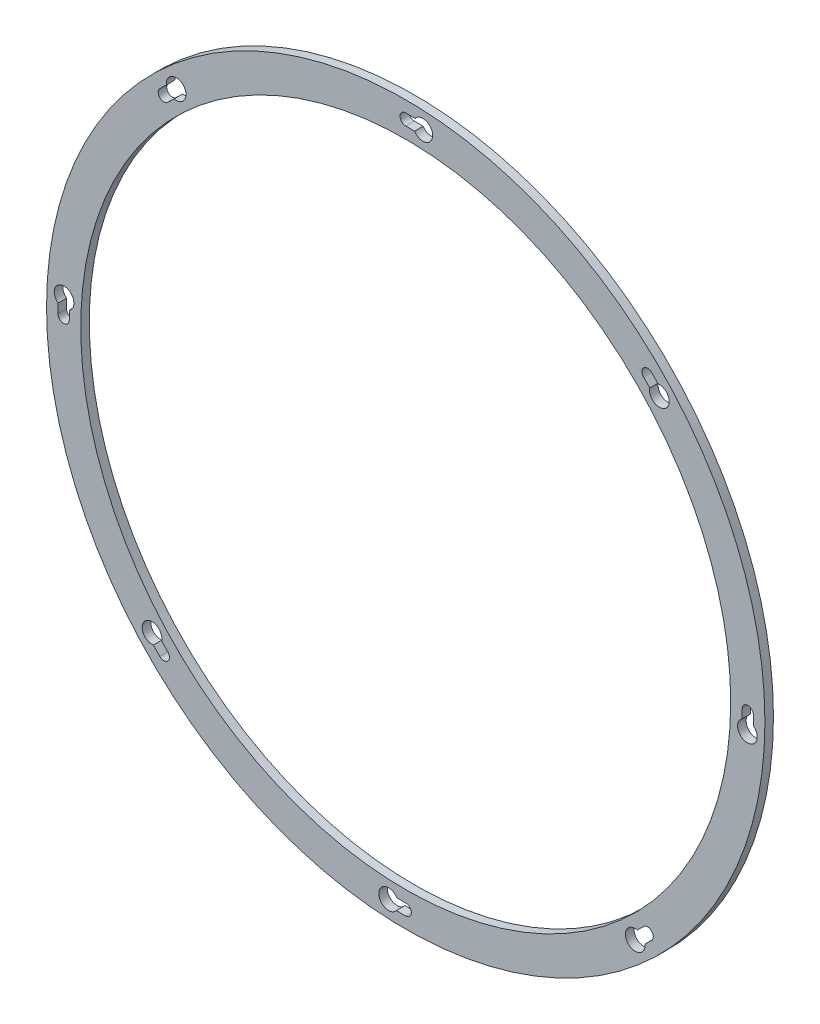
SolidWorks part; units mm, degrees
material "6061 Alloy"
ref_plane "Front Plane" through (0, 0, 0) normal (0, 0, 1) x (1, 0, 0)
ref_plane "Top Plane" through (0, 0, 0) normal (0, 1, 0) x (1, 0, 0)
ref_plane "Right Plane" through (0, 0, 0) normal (1, 0, 0) x (0, 0, -1)
sketch "Sketch1" plane through (0, 0, 0) normal (0, 0, 1) x (1, 0, 0)
  circle A0 centre (0, 0) radius 190
  circle A1 centre (0, 0) radius 210
  dimension "D1" = 380
  dimension "D2" = 20
extrude "Boss-Extrude1" add sketch "Sketch1" along normal blind 5
hole_wizard "M6 Clearance Hole1" positions "Sketch2" profile "Sketch3" hole size "M6" standard "ISO" end condition through all
sketch "Sketch2" plane through (0, 0, 5) normal (0, 0, 1) x (1, 0, 0)
  line L0 (0, 0) -> (0, 200) construction
  line L1 (0, 200) -> (0, 210) construction
  circle A0 centre (0, 0) radius 210 construction
  point P0 (0, 200)
  dimension "D1" = 10
sketch "Sketch3" plane through (0, 200, 5) normal (1, 0, 0) x (0, -1, 0)
  line L0 (0, 0) -> (0, 5)
  line L1 (0, 5) -> (3.3, 5)
  line L2 (3.3, 5) -> (3.3, 0)
  line L5 (3.3, 0) -> (0, 0)
  line L11 (0, -6.35) -> (0, 107.95) construction
  dimension "Thru Hole Dia." = 6.6
  dimension "Thru Hole Depth" = 5
sketch "Sketch4" plane through (0, 0, 5) normal (0, 0, 1) x (1, 0, 0)
  circle A0 centre (0, 0) radius 200 construction
  arc A1 (5.1656, 196.6322) -> (5.4179, 203.2278) centre (9.9969, 199.75) ccw
  arc A2 (5.1656, 196.6322) -> (0, 196.7) centre (0, 0) ccw
  arc A3 (5.4179, 203.2278) -> (0, 203.3) centre (0, 0) ccw
  circle A4 centre (0, 200) radius 3.3 construction
  arc A5 (0, 196.7) -> (0, 203.3) centre (0, 200) ccw
  point P10 (0, 203.3)
  point P11 (0, 196.7)
  dimension "D1" = 11.5
  dimension "D2" = 10
extrude "Cut-Extrude1" cut sketch "Sketch4" against normal blind 5
pattern_circular "CirPattern1" count 8 over 360 about axis through (0, 0, 0) along (0, 0, 1) of "M6 Clearance Hole1", "Cut-Extrude1"
